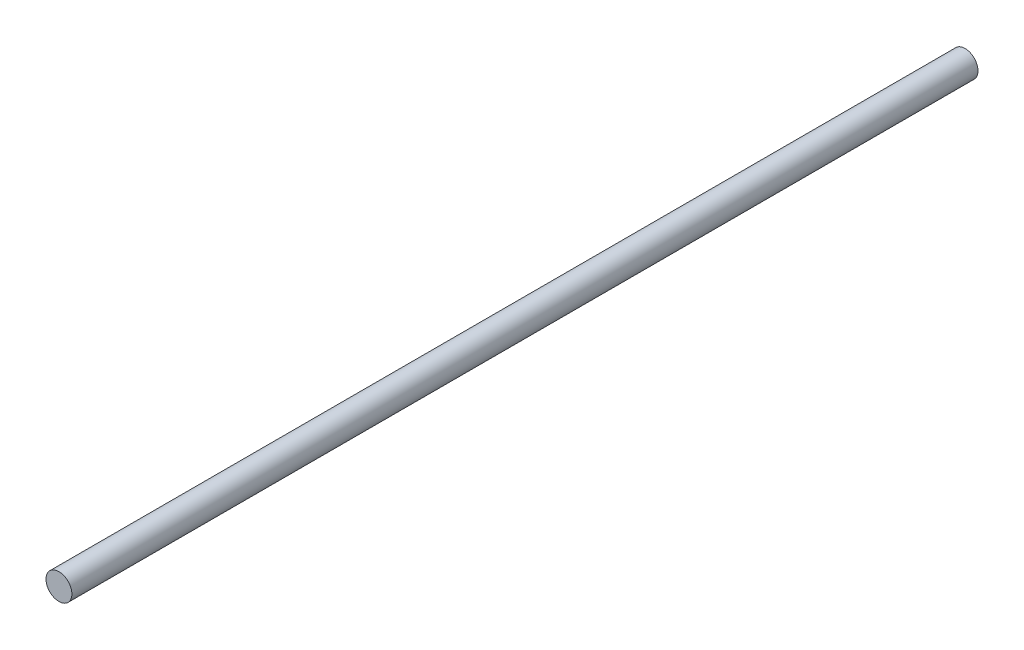
SolidWorks part; units mm, degrees
ref_plane "Plano frontal" through (0, 0, 0) normal (0, 0, 1) x (1, 0, 0)
ref_plane "Plano superior" through (0, 0, 0) normal (0, 1, 0) x (1, 0, 0)
ref_plane "Plano direito" through (0, 0, 0) normal (1, 0, 0) x (0, 0, -1)
sketch "Esboço1" plane through (0, 0, 0) normal (0, 0, 1) x (1, 0, 0)
  circle A0 centre (0, 0) radius 4
  dimension "D1" = 8
extrude "Ressalto-extrusão1" add sketch "Esboço1" along normal blind 280
